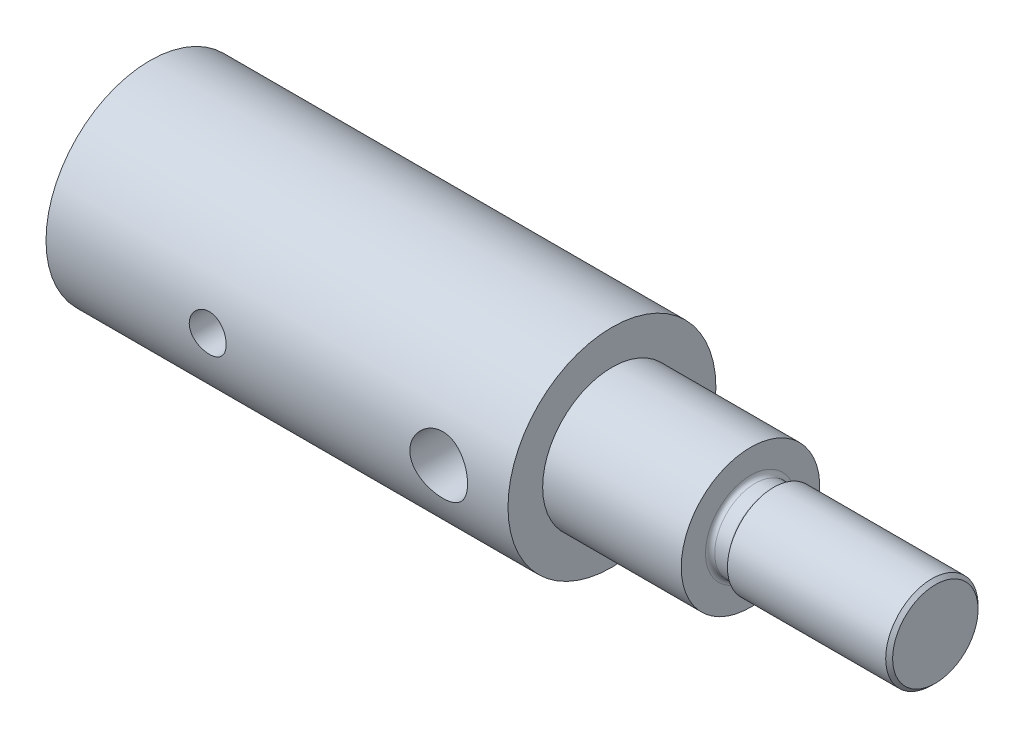
SolidWorks part; units mm, degrees
material "3.0205 (EN-AW 1200)"
ref_plane "Vorne" through (0, 0, 0) normal (0, 0, 1) x (1, 0, 0)
ref_plane "Oben" through (0, 0, 0) normal (0, 1, 0) x (1, 0, 0)
ref_plane "Rechts" through (0, 0, 0) normal (1, 0, 0) x (0, 0, -1)
sketch "Skizze1" plane through (0, 0, 0) normal (0, 0, 1) x (1, 0, 0)
  line L0 (0, 0) -> (71.7919, 0) construction
  line L1 (0, 4.5) -> (0, 2)
  line L2 (0, 2) -> (14, 2)
  line L3 (14, 2) -> (15.2017, 0)
  line L4 (15.2017, 0) -> (34, 0)
  line L5 (26, 2) -> (26, 3)
  line L6 (26, 3) -> (20, 3)
  line L7 (20, 3) -> (20, 4.5)
  line L8 (20, 4.5) -> (0, 4.5)
  line L9 (26, 2) -> (34, 2)
  line L10 (34, 2) -> (34, 0)
  dimension "D1" = 4
  dimension "D2" = 6
  dimension "D3" = 6
  dimension "D4" = 59
  dimension "D5" = 14
  dimension "D6" = 9
  dimension "D7" = 20
  dimension "D8" = 8
  dimension "D9" = 4
revolve "Rotation1" add sketch "Skizze1" angle 360 about L0
cosmetic thread "Gewindedarstellung1" parameters "D2"=3.76
ref_plane "Ebene1" through (0, 0, -4.5) normal (0, 0, -1) x (-1, 0, 0)
chamfer "Fase1" distance 0.15 angle 45 1 edges at (34, 0, 2)
sketch "Skizze2" plane through (0, 0, 0) normal (0, 0, 1) x (1, 0, 0)
  line L0 (26, 2.25) -> (27, 2.25)
  line L1 (26, 2.25) -> (26, 1.75)
  line L2 (27, 2.25) -> (27, 1.75)
  line L3 (26, 1.75) -> (27, 1.75)
  line L4 (26, -3) -> (26, 3) construction
  line L5 (0, 0) -> (35.0484, 0) construction
  dimension "D1" = 3.5
  dimension "D2" = 0.5
  dimension "D3" = 1
revolve "Schnitt-Rotation1" cut sketch "Skizze2" angle 360 about L5
fillet "Verrundung1" radius 0.2 2 edges at (27, 0, 1.75) (26, 0, 1.75)
hole_wizard "M2 Gewindebohrung1" positions "Skizze6" profile "Skizze5" tap size "M2" standard "Iso"
sketch "Skizze6" plane through (0, 0, 0) normal (0, 0, 1) x (1, 0, 0)
  point P0 (7, 0)
  dimension "D1" = 7
sketch "Skizze5" plane through (7, 0, 0) normal (1, 0, 0) x (0, 1, 0)
  line L0 (0, 0) -> (0, 4.5)
  line L1 (0, 4.5) -> (0.8, 4.5)
  line L2 (0.8, 4.5) -> (0.8, 0)
  line L5 (0.8, 0) -> (0, 0)
  line L11 (0, -6.35) -> (0, 107.95) construction
  dimension "Nenndurchmesser (Haupt)" = 1.6
  dimension "Bohrungstiefe" = 4.5
cosmetic thread "Gewindedarstellung2" parameters "D2"=2
sketch "Skizze7" plane through (0, 0, 0) normal (0, 0, 1) x (1, 0, 0)
  circle A0 centre (17, 0) radius 1.25
  dimension "D1" = 2.5
  dimension "D2" = 17
extrude "Schnitt-Linear austragen2" cut sketch "Skizze7" against normal through all and the other way through all
move or copy body "Körper-Verschieben/Kopieren1" [suppressed] bodies to move or copy 107
